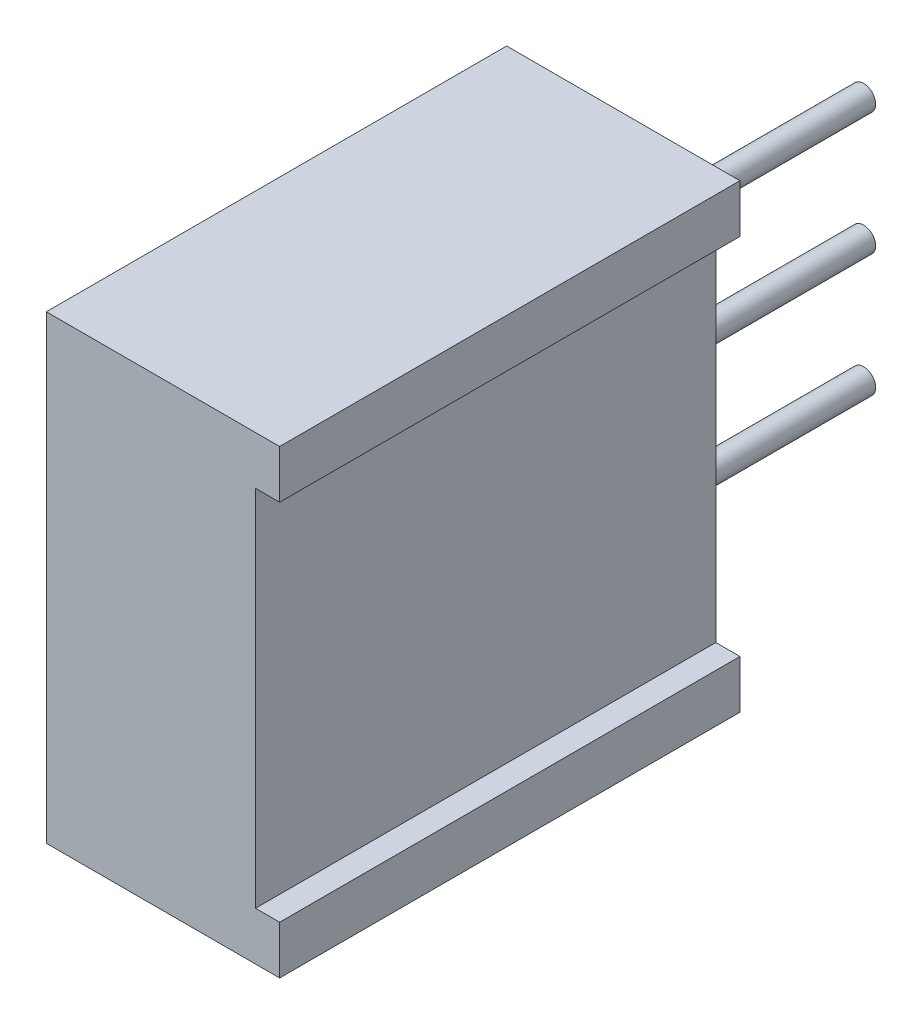
SolidWorks part; units mm, degrees
ref_plane "Front Plane" through (0, 0, 0) normal (0, 0, 1) x (1, 0, 0)
ref_plane "Top Plane" through (0, 0, 0) normal (0, 1, 0) x (1, 0, 0)
ref_plane "Right Plane" through (0, 0, 0) normal (1, 0, 0) x (0, 0, -1)
sketch "Sketch1" plane through (0, 0, 0) normal (1, 0, 0) x (0, 0, 1)
  line L0 (0, 0) -> (9.53, 0)
  line L1 (0, 0) -> (0, 9.53)
  line L2 (9.53, 9.53) -> (0, 9.53)
  line L3 (9.53, 9.53) -> (9.53, 0)
  dimension "D1" = 9.53
extrude "Basic Shape" add sketch "Sketch1" along normal blind 4.83
sketch "Sketch3" plane through (0, 0, 0) normal (1, 0, 0) x (0, 1, 0)
  line L0 (-9.53, 9.53) -> (0, 9.53) construction
  line L1 (0, 0) -> (0, 9.53) construction
  circle A0 centre (-4.765, 4.765) radius 2
  point P2 (-4.765, 9.53)
  point P3 (0, 4.765)
  dimension "D1" = 4
extrude "Adjuster" cut sketch "Sketch3" along normal blind 0.1
sketch "Sketch4" plane through (0.1, 0, 0) normal (-1, 0, 0) x (0, -1, 0)
  line L0 (3.7492, 6.4879) -> (6.4879, 3.7492)
  line L1 (3.0421, 5.7808) -> (5.7808, 3.0421)
  line L2 (5.1186, 5.1186) -> (4.4114, 4.4114) construction
  line L3 (9.53, 9.53) -> (0, 9.53) construction
  circle A0 centre (4.765, 4.765) radius 2 construction
  circle A1 centre (4.765, 4.765) radius 2 construction
  arc A3 (3.7492, 6.4879) -> (3.0421, 5.7808) centre (4.765, 4.765) ccw
  arc A4 (5.7808, 3.0421) -> (6.4879, 3.7492) centre (4.765, 4.765) ccw
  point P6 (4.765, 4.765)
  dimension "D2" = 45
  dimension "D1" = 1
extrude "Adjuster Slot" cut sketch "Sketch4" against normal blind 1
sketch "Sketch5" plane through (0, -19.06, 0) normal (0, 0, -1) x (0, -1, 0)
  line L0 (-9.53, 0) -> (-19.06, 0) construction
  line L1 (-14.295, -1.1) -> (-14.295, -0.1) construction
  line L2 (-19.06, -4.83) -> (-9.53, -4.83) construction
  circle A0 centre (-16.835, -2.39) radius 0.25
  circle A1 centre (-14.295, -2.39) radius 0.25
  circle A2 centre (-11.755, -2.39) radius 0.25
  point P8 (-14.295, 0)
  dimension "D4" = 0.5
  dimension "D1" = 2.44
  dimension "D3" = 2.54
  dimension "D5" = 2.54
extrude "Pins" add sketch "Sketch5" along normal blind 5
sketch "Sketch6" plane through (0, 0, 9.53) normal (0, 0, 1) x (1, 0, 0)
  line L0 (4.83, 0) -> (4.83, -9.53) construction
  line L3 (4.33, -8.53) -> (4.33, -1)
  line L4 (4.83, -1) -> (0, -1)
  line L5 (4.33, -1) -> (4.83, -1)
  line L6 (4.83, -8.53) -> (0, -8.53)
  line L7 (4.33, -8.53) -> (4.83, -8.53)
  line L9 (4.83, -8.53) -> (4.83, -1)
  dimension "D1" = 0.5
  dimension "D2" = 1
  dimension "D3" = 1
extrude "Rear Relief" cut sketch "Sketch6" against normal through all
ref_plane "Board Plane" through (0, 0, -1) normal (0, 0, 1) x (1, 0, 0)
sketch "Component_Outline" plane through (0, 0, -1) normal (0, 0, 1) x (1, 0, 0)
  line L0 (0, 0) -> (0, -9.53)
  line L1 (0, -9.53) -> (4.83, -9.53)
  line L2 (4.83, -9.53) -> (4.83, -8.53)
  line L3 (4.83, -8.53) -> (4.33, -8.53)
  line L4 (4.33, -8.53) -> (4.33, -1)
  line L5 (4.33, -1) -> (4.83, -1)
  line L6 (4.83, -1) -> (4.83, 0)
  line L7 (4.83, 0) -> (0, 0)
